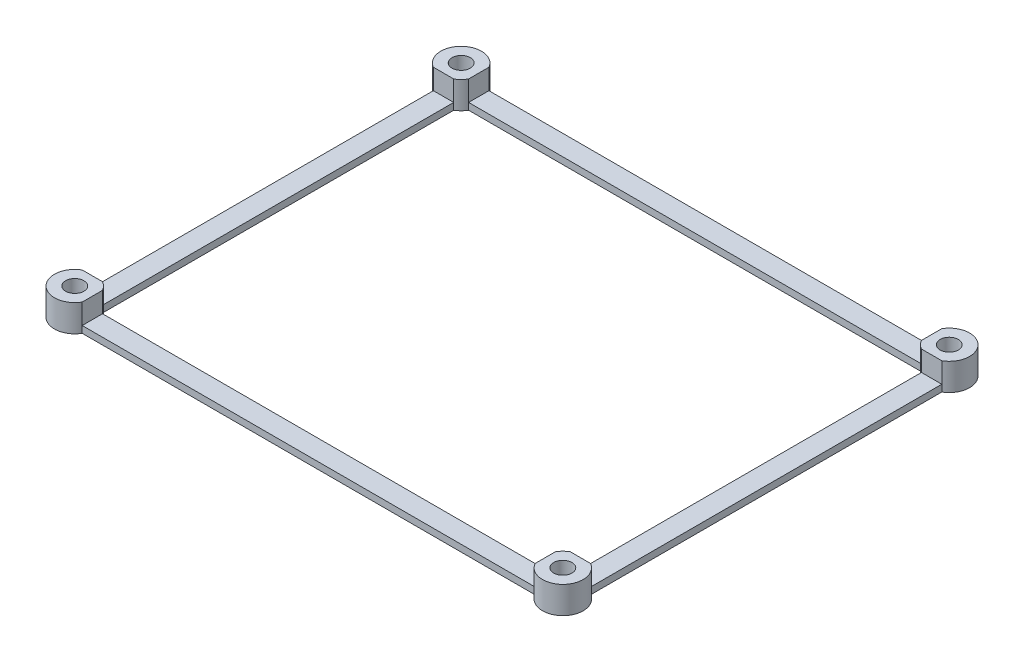
SolidWorks part; units mm, degrees
ref_plane "Front Plane" through (0, 0, 0) normal (0, 0, 1) x (1, 0, 0)
ref_plane "Top Plane" through (0, 0, 0) normal (0, 1, 0) x (1, 0, 0)
ref_plane "Right Plane" through (0, 0, 0) normal (1, 0, 0) x (0, 0, -1)
sketch "Sketch1" plane through (0, 0, 0) normal (0, 1, 0) x (1, 0, 0)
  line L1 (-36, -28.5) -> (36, -28.5) construction
  line L2 (-36, -28.5) -> (-36, 28.5) construction
  line L3 (-36, 28.5) -> (36, 28.5) construction
  line L4 (36, -28.5) -> (36, 28.5) construction
  line L5 (-36, -28.5) -> (36, 28.5) construction
  line L6 (-36, 28.5) -> (36, -28.5) construction
  line L7 (-33.4019, 27) -> (33.4019, 27)
  line L9 (-33.4019, 30) -> (33.4019, 30)
  line L11 (-33.4019, 27) -> (33.4019, 30) construction
  line L12 (-33.4019, 30) -> (33.4019, 27) construction
  line L14 (-37.5, -25.9019) -> (-37.5, 25.9019)
  line L16 (-34.5, -25.9019) -> (-34.5, 25.9019)
  line L17 (-37.5, -25.9019) -> (-34.5, 25.9019) construction
  line L18 (-37.5, 25.9019) -> (-34.5, -25.9019) construction
  line L20 (34.5, -25.9019) -> (34.5, 25.9019)
  line L22 (37.5, -25.9019) -> (37.5, 25.9019)
  line L23 (34.5, -25.9019) -> (37.5, 25.9019) construction
  line L24 (34.5, 25.9019) -> (37.5, -25.9019) construction
  line L25 (-33.4019, -30) -> (33.4019, -30)
  line L27 (-33.4019, -27) -> (33.4019, -27)
  line L29 (-33.4019, -30) -> (33.4019, -27) construction
  line L30 (-33.4019, -27) -> (33.4019, -30) construction
  circle A0 centre (36, 28.5) radius 1.35
  circle A1 centre (36, -28.5) radius 1.35
  circle A2 centre (-36, -28.5) radius 1.35
  circle A3 centre (-36, 28.5) radius 1.35
  arc A4 (-34.5, 25.9019) -> (-33.4019, 27) centre (-36, 28.5) ccw
  arc A5 (33.4019, 27) -> (34.5, 25.9019) centre (36, 28.5) ccw
  arc A6 (34.5, -25.9019) -> (33.4019, -27) centre (36, -28.5) ccw
  arc A7 (-33.4019, -27) -> (-34.5, -25.9019) centre (-36, -28.5) ccw
  arc A8 (-37.5, -25.9019) -> (-33.4019, -30) centre (-36, -28.5) ccw
  arc A9 (-33.4019, 30) -> (-37.5, 25.9019) centre (-36, 28.5) ccw
  arc A10 (37.5, 25.9019) -> (33.4019, 30) centre (36, 28.5) ccw
  arc A11 (33.4019, -30) -> (37.5, -25.9019) centre (36, -28.5) ccw
  point P0 (0, 0)
  point P14 (0, 28.5)
  point P19 (-36, 0)
  point P24 (36, 0)
  point P29 (0, -28.5)
  dimension "D3" = 2.7
  dimension "D4" = 6
  dimension "D1" = 72
  dimension "D2" = 57
  dimension "D5" = 3
  dimension "D6" = 3
  dimension "D7" = 3
  dimension "D8" = 3
extrude "Boss-Extrude1" add sketch "Sketch1" along normal blind 4
sketch "Sketch2" plane through (0, 4, 0) normal (0, 1, 0) x (1, 0, 0)
  line L1 (-37.5, 25.9019) -> (-34.5, 25.9019)
  line L2 (-37.5, 25.9019) -> (-37.5, -25.9019)
  line L3 (-37.5, -25.9019) -> (-34.5, -25.9019)
  line L4 (-34.5, 25.9019) -> (-34.5, -25.9019)
  line L5 (-33.4019, -27) -> (33.4019, -27)
  line L6 (-33.4019, -27) -> (-33.4019, -30)
  line L7 (-33.4019, -30) -> (33.4019, -30)
  line L8 (33.4019, -27) -> (33.4019, -30)
  line L9 (34.5, -25.9019) -> (37.5, -25.9019)
  line L10 (34.5, -25.9019) -> (34.5, 25.9019)
  line L11 (34.5, 25.9019) -> (37.5, 25.9019)
  line L12 (37.5, -25.9019) -> (37.5, 25.9019)
  line L13 (33.4019, 27) -> (-33.4019, 27)
  line L14 (33.4019, 27) -> (33.4019, 30)
  line L15 (33.4019, 30) -> (-33.4019, 30)
  line L16 (-33.4019, 27) -> (-33.4019, 30)
extrude "Cut-Extrude1" cut sketch "Sketch2" against normal offset from surface (3 mm away) 1 up to face at (-36, 0, -27.15)
